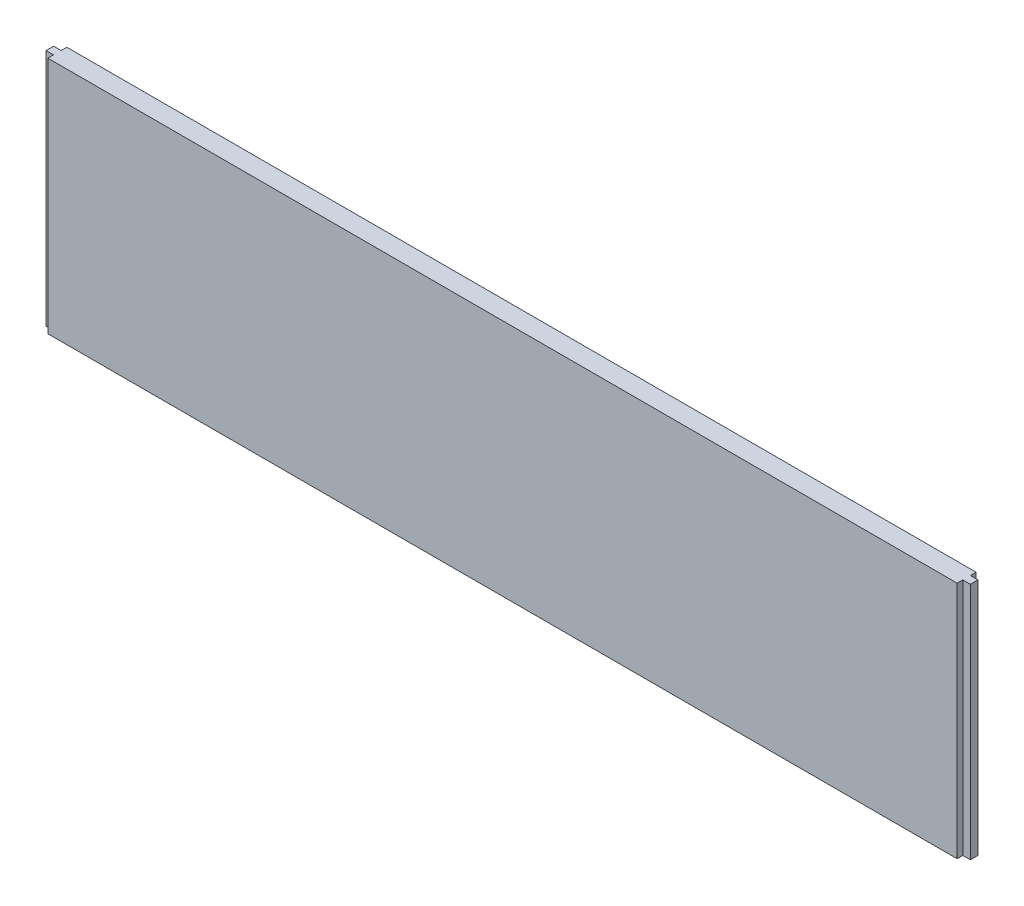
SolidWorks part; units mm, degrees
ref_plane "Front Plane" through (0, 0, 0) normal (0, 0, 1) x (1, 0, 0)
ref_plane "Top Plane" through (0, 0, 0) normal (0, 1, 0) x (1, 0, 0)
ref_plane "Right Plane" through (0, 0, 0) normal (1, 0, 0) x (0, 0, -1)
sketch "Sketch1" plane through (0, 0, 0) normal (0, 0, 1) x (1, 0, 0)
  line L1 (0, 0) -> (774.7, 0)
  line L2 (0, 0) -> (0, 200.025)
  line L3 (0, 200.025) -> (774.7, 200.025)
  line L4 (774.7, 0) -> (774.7, 200.025)
  dimension "D1" = 774.7
  dimension "D2" = 200.025
extrude "Boss-Extrude1" add sketch "Sketch1" along normal blind 15.875
sketch "Sketch2" plane through (0, 200.025, 0) normal (0, 1, 0) x (1, 0, 0)
  line L0 (-225.3, -7.9375) -> (49774.7, -7.9375) construction
  line L1 (774.7, -15.875) -> (768.35, -15.875)
  line L2 (774.7, -15.875) -> (774.7, -11.1125)
  line L3 (774.7, -11.1125) -> (768.35, -11.1125)
  line L4 (768.35, -15.875) -> (768.35, -11.1125)
  line L5 (774.7, -15.875) -> (774.7, 0) construction
  line L6 (387.35, -1019.05) -> (387.35, 48980.95) construction
  line L7 (774.7, -15.875) -> (0, -15.875) construction
  line L8 (768.35, 0) -> (768.35, -4.7625)
  line L9 (774.7, -4.7625) -> (768.35, -4.7625)
  line L10 (774.7, 0) -> (774.7, -4.7625)
  line L11 (774.7, 0) -> (768.35, 0)
  line L12 (0, 0) -> (6.35, 0)
  line L13 (0, 0) -> (0, -4.7625)
  line L14 (0, -4.7625) -> (6.35, -4.7625)
  line L15 (6.35, 0) -> (6.35, -4.7625)
  line L16 (6.35, -15.875) -> (6.35, -11.1125)
  line L17 (0, -11.1125) -> (6.35, -11.1125)
  line L18 (0, -15.875) -> (0, -11.1125)
  line L19 (0, -15.875) -> (6.35, -15.875)
  point P10 (774.7, -7.9375)
  point P15 (387.35, -15.875)
  dimension "D1" = 6.35
extrude "Cut-Extrude1" cut sketch "Sketch2" against normal through all
